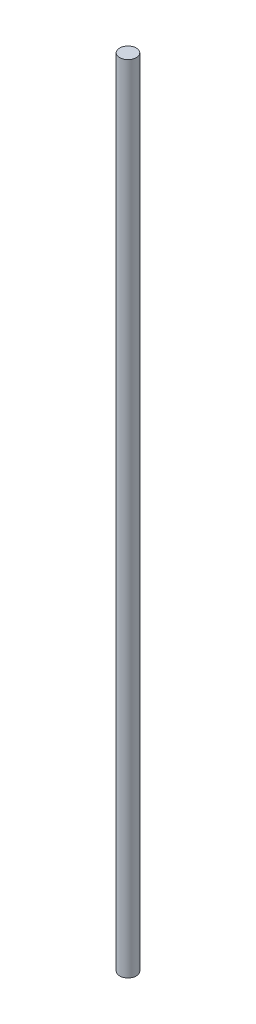
SolidWorks part; units mm, degrees
material "Stainless Steel (ferritic)"
ref_plane "Front Plane" through (0, 0, 0) normal (0, 0, 1) x (1, 0, 0)
ref_plane "Top Plane" through (0, 0, 0) normal (0, 1, 0) x (1, 0, 0)
ref_plane "Right Plane" through (0, 0, 0) normal (1, 0, 0) x (0, 0, -1)
sketch "Sketch1" plane through (0, 0, 0) normal (0, 1, 0) x (1, 0, 0)
  circle A0 centre (0, 0) radius 5
  dimension "D1" = 10
extrude "Boss-Extrude1" add sketch "Sketch1" along normal blind 477
